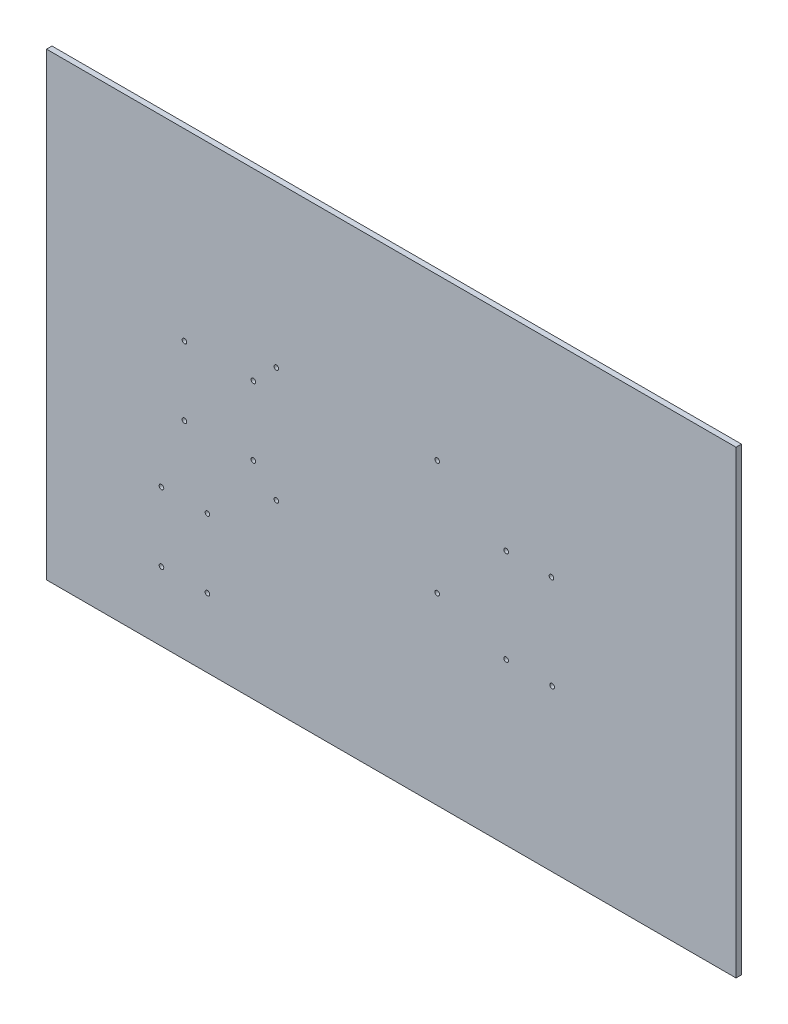
SolidWorks part; units mm, degrees
ref_plane "Front Plane" through (0, 0, 0) normal (0, 0, 1) x (1, 0, 0)
ref_plane "Top Plane" through (0, 0, 0) normal (0, 1, 0) x (1, 0, 0)
ref_plane "Right Plane" through (0, 0, 0) normal (1, 0, 0) x (0, 0, -1)
sketch "Sketch2" plane through (0, 0, 0) normal (0, 0, 1) x (1, 0, 0)
  line L0 (0, 254) -> (0, -254) construction
  line L1 (-381, -254) -> (381, -254)
  line L2 (-381, -254) -> (-381, 254)
  line L3 (-381, 254) -> (381, 254)
  line L4 (381, -254) -> (381, 254)
  line L5 (-381, -254) -> (381, 254) construction
  line L6 (-381, 254) -> (381, -254) construction
  line L7 (-304.8, 254) -> (-304.8, -254) construction
  line L8 (-355.6, 254) -> (-355.6, -254) construction
  line L9 (-330.2, 254) -> (-330.2, -254) construction
  line L10 (-279.4, 254) -> (-279.4, -254) construction
  line L11 (-254, 254) -> (-254, -254) construction
  line L12 (-228.6, 254) -> (-228.6, -254) construction
  line L13 (-203.2, 254) -> (-203.2, -254) construction
  line L14 (-177.8, 254) -> (-177.8, -254) construction
  line L15 (-152.4, 254) -> (-152.4, -254) construction
  line L16 (-127, 254) -> (-127, -254) construction
  line L17 (-101.6, 254) -> (-101.6, -254) construction
  line L18 (-76.2, 254) -> (-76.2, -254) construction
  line L19 (-50.8, 254) -> (-50.8, -254) construction
  line L20 (-25.4, 254) -> (-25.4, -254) construction
  line L21 (25.4, 254) -> (25.4, -254) construction
  line L22 (50.8, 254) -> (50.8, -254) construction
  line L23 (76.2, 254) -> (76.2, -254) construction
  line L24 (101.6, 254) -> (101.6, -254) construction
  line L25 (127, 254) -> (127, -254) construction
  line L26 (152.4, 254) -> (152.4, -254) construction
  line L27 (177.8, 254) -> (177.8, -254) construction
  line L28 (203.2, 254) -> (203.2, -254) construction
  line L29 (228.6, 254) -> (228.6, -254) construction
  line L30 (254, 254) -> (254, -254) construction
  line L31 (279.4, 254) -> (279.4, -254) construction
  line L32 (304.8, 254) -> (304.8, -254) construction
  line L33 (330.2, 254) -> (330.2, -254) construction
  line L34 (355.6, 254) -> (355.6, -254) construction
  line L35 (-381, 0) -> (381, 0) construction
  line L36 (-381, 152.4) -> (381, 152.4) construction
  line L37 (-381, 177.8) -> (381, 177.8) construction
  line L38 (-381, 203.2) -> (381, 203.2) construction
  line L39 (-381, 228.6) -> (381, 228.6) construction
  line L40 (-381, 127) -> (381, 127) construction
  line L41 (-381, 101.6) -> (381, 101.6) construction
  line L42 (-381, 76.2) -> (381, 76.2) construction
  line L43 (-381, 50.8) -> (381, 50.8) construction
  line L44 (-381, 25.4) -> (381, 25.4) construction
  line L45 (-381, -25.4) -> (381, -25.4) construction
  line L46 (-381, -50.8) -> (381, -50.8) construction
  line L47 (-381, -76.2) -> (381, -76.2) construction
  line L48 (-381, -101.6) -> (381, -101.6) construction
  line L49 (-381, -127) -> (381, -127) construction
  line L50 (-381, -152.4) -> (381, -152.4) construction
  line L51 (-381, -177.8) -> (381, -177.8) construction
  line L52 (-381, -203.2) -> (381, -203.2) construction
  line L53 (-381, -228.6) -> (381, -228.6) construction
  line L54 (-381, 12.7) -> (381, 12.7) construction
  circle A0 centre (-228.6, 50.8) radius 2.555
  circle A1 centre (-228.6, -25.4) radius 2.555
  circle A2 centre (-152.4, 50.8) radius 2.555
  circle A3 centre (-152.4, -25.4) radius 2.555
  circle A5 centre (-127, 76.2) radius 2.555
  circle A6 centre (-127, -50.8) radius 2.555
  circle A9 centre (50.8, 76.2) radius 2.555
  circle A10 centre (50.8, -50.8) radius 2.555
  circle A11 centre (-254, -177.8) radius 2.555
  circle A12 centre (-203.2, -177.8) radius 2.555
  circle A13 centre (-254, -101.6) radius 2.555
  circle A14 centre (-203.2, -101.6) radius 2.555
  circle A15 centre (127, -76.2) radius 2.555
  circle A16 centre (177.8, -76.2) radius 2.555
  circle A17 centre (127, 27.7) radius 2.555
  circle A18 centre (177, 27.6969) radius 2.555
  point P0 (0, 0)
  point P132 (182.0847, 27.7)
  point P133 (173.9091, 27.7)
  dimension "D17" = 5.11
  dimension "D18" = 5.11
  dimension "D19" = 5.11
  dimension "D20" = 5.11
  dimension "D22" = 5.11
  dimension "D23" = 5.11
  dimension "D24" = 5.11
  dimension "D25" = 5.11
  dimension "D26" = 5.11
  dimension "D27" = 5.11
  dimension "D28" = 5.11
  dimension "D29" = 5.11
  dimension "D31" = 5.11
  dimension "D30" = 5.11
  dimension "D34" = 5.11
  dimension "D35" = 5.11
  dimension "D1" = 762
  dimension "D2" = 508
  dimension "D3" = 25.4
  dimension "D4" = 25.4
  dimension "D5" = 25.4
  dimension "D6" = 25.4
  dimension "D7" = 25.4
  dimension "D8" = 25.4
  dimension "D9" = 25.4
  dimension "D10" = 25.4
  dimension "D11" = 25.4
  dimension "D12" = 25.4
  dimension "D13" = 25.4
  dimension "D14" = 25.4
  dimension "D15" = 25.4
  dimension "D16" = 25.4
  dimension "D21" = 12.7
  dimension "D32" = 103.9
  dimension "D33" = 103.9
  dimension "D36" = 0.8
extrude "Boss-Extrude1" add sketch "Sketch2" along normal blind 6
